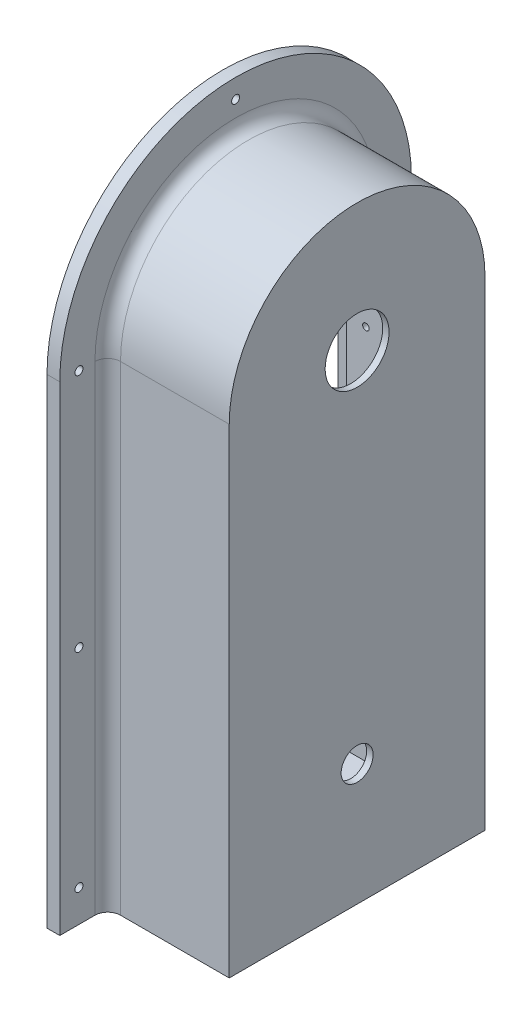
SolidWorks part; units mm, degrees
ref_plane "정면" through (0, 0, 0) normal (0, 0, 1) x (1, 0, 0)
ref_plane "윗면" through (0, 0, 0) normal (0, 1, 0) x (1, 0, 0)
ref_plane "우측면" through (0, 0, 0) normal (1, 0, 0) x (0, 0, -1)
ref_plane "평면1" through (0, 35.25, 0) normal (0, -1, 0) x (1, 0, 0)
sketch "스케치1" plane through (0, 35.25, 0) normal (0, -1, 0) x (1, 0, 0)
  line L0 (-19, -14.25) -> (-23, -14.25)
  line L1 (-23, -14.25) -> (-23, -69.25)
  line L2 (-23, -69.25) -> (-19, -69.25)
  line L3 (-19, -69.25) -> (-19, -14.25)
  line L4 (-18.9999, -14.25) -> (-23.0001, -14.25) construction
revolve "회전1" add sketch "스케치1" angle 180 about L4
sketch "스케치2" plane through (0, 35.25, 0) normal (0, -1, 0) x (1, 0, 0)
  line L0 (-19, -69.25) -> (-23, -69.25)
  line L1 (-23, -69.25) -> (-23, 40.75)
  line L2 (-23, 40.75) -> (-19, 40.75)
  line L3 (-19, 40.75) -> (-19, -69.25)
extrude "보스-돌출1" add sketch "스케치2" along normal blind 150
sketch "스케치3" plane through (-19, 0, 0) normal (1, 0, 0) x (0, 0, -1)
  line L0 (-25.75, -114.75) -> (-25.75, 35.25)
  line L1 (54.25, 35.25) -> (54.25, -114.75)
  line L2 (54.25, -114.75) -> (-25.75, -114.75)
  arc A0 (-25.75, 35.25) -> (54.25, 35.25) centre (14.25, 35.25) cw
extrude "보스-돌출2" add sketch "스케치3" along normal blind 38
sketch "스케치4" plane through (-23, 0, 0) normal (-1, 0, 0) x (0, 0, 1)
  line L0 (-50.25, -110.75) -> (21.75, -110.75)
  line L1 (21.75, -110.75) -> (21.75, 35.25)
  line L2 (-50.25, 35.25) -> (-50.25, -110.75)
  arc A0 (21.75, 35.25) -> (-50.25, 35.25) centre (-14.25, 35.25) ccw
extrude "컷-돌출1" cut sketch "스케치4" against normal blind 40
sketch "스케치5" plane through (17, 0, 0) normal (-1, 0, 0) x (0, 0, 1)
  line L0 (4, 50.5) -> (4, -4)
  line L1 (4, -4) -> (-32.5, -4)
  line L2 (-32.5, -4) -> (-32.5, 50.5)
  line L3 (-32.5, 50.5) -> (4, 50.5)
extrude "보스-돌출3" add sketch "스케치5" along normal blind 17
sketch "스케치6" plane through (0, 0, 0) normal (-1, 0, 0) x (0, 0, 1)
  line L0 (-30, -1.5) -> (1.5, -1.5)
  line L1 (1.5, -1.5) -> (1.5, 48)
  line L2 (1.5, 48) -> (-30, 48)
  line L3 (-30, 48) -> (-30, -1.5)
extrude "컷-돌출2" cut sketch "스케치6" against normal blind 17
hole_wizard "Ø20.0 (20) 지름 구멍1" positions "스케치8" profile "스케치7" hole size "Ø20.0" standard "Ansi Metric"
sketch "스케치8" plane through (17, 0, 0) normal (-1, 0, 0) x (0, 0, 1)
  point P0 (-14.25, 35.25)
sketch "스케치7" plane through (17, 35.25, -14.25) normal (0, 1, 0) x (0, 0, 1)
  line L0 (0, 0) -> (0, 2)
  line L1 (0, 2) -> (10, 2)
  line L2 (10, 2) -> (10, 0)
  line L5 (10, 0) -> (0, 0)
  line L11 (0, -6.35) -> (0, 107.95) construction
  dimension "관통 구멍 지름" = 20
  dimension "관통 구멍 깊이" = 2
hole_wizard "Ø10.0 (10) 지름 구멍1" positions "스케치10" profile "스케치9" hole size "Ø10.0" standard "Ansi Metric"
sketch "스케치10" plane through (17, 0, 0) normal (-1, 0, 0) x (0, 0, 1)
  point P0 (-14.25, -76.75)
sketch "스케치9" plane through (17, -76.75, -14.25) normal (0, 1, 0) x (0, 0, 1)
  line L0 (0, 0) -> (0, 2)
  line L1 (0, 2) -> (5, 2)
  line L2 (5, 2) -> (5, 0)
  line L5 (5, 0) -> (0, 0)
  line L11 (0, -6.35) -> (0, 107.95) construction
  dimension "관통 구멍 지름" = 10
  dimension "관통 구멍 깊이" = 2
hole_wizard "Ø2.5 (2.5) 지름 구멍1" positions "스케치12" profile "스케치11" hole size "Ø2.5" standard "Ansi Metric"
sketch "스케치12" plane through (-19, 0, 0) normal (1, 0, 0) x (0, 0, -1)
  point P0 (-34.75, -104.75)
  point P1 (63.25, -104.75)
  point P2 (63.25, -39.75)
  point P3 (63.25, 35.25)
  point P4 (-34.75, 35.25)
  point P5 (-34.75, -39.75)
  point P6 (14.25, 84.25)
sketch "스케치11" plane through (-19, -104.75, 34.75) normal (0, 1, 0) x (0, 0, -1)
  line L0 (0, 0) -> (0, 4)
  line L1 (0, 4) -> (1.25, 4)
  line L2 (1.25, 4) -> (1.25, 0)
  line L5 (1.25, 0) -> (0, 0)
  line L11 (0, -6.35) -> (0, 107.95) construction
  dimension "관통 구멍 지름" = 2.5
  dimension "관통 구멍 깊이" = 4
hole_wizard "Ø2.05 (2.05) 지름 구멍1" positions "스케치14" profile "스케치13" hole size "Ø2.05" standard "Ansi Metric"
sketch "스케치14" plane through (0, -1.5, 0) normal (0, 1, 0) x (1, 0, 0)
  point P0 (6, 6.25)
  point P1 (6, 22.25)
sketch "스케치13" plane through (6, -1.5, -6.25) normal (1, 0, 0) x (0, 0, 1)
  line L0 (0, 0) -> (0, 2.5)
  line L1 (0, 2.5) -> (1.025, 2.5)
  line L2 (1.025, 2.5) -> (1.025, 0)
  line L5 (1.025, 0) -> (0, 0)
  line L11 (0, -6.35) -> (0, 107.95) construction
  dimension "관통 구멍 지름" = 2.05
  dimension "관통 구멍 깊이" = 2.5
hole_wizard "Ø2.05 (2.05) 지름 구멍2" positions "스케치16" profile "스케치15" hole size "Ø2.05" standard "Ansi Metric"
sketch "스케치16" plane through (0, 0, 1.5) normal (0, 0, -1) x (-1, 0, 0)
  point P0 (-6, 27.25)
  point P1 (-6, 3.25)
sketch "스케치15" plane through (6, 27.25, 1.5) normal (1, 0, 0) x (0, 1, 0)
  line L0 (0, 0) -> (0, 2.5)
  line L1 (0, 2.5) -> (1.025, 2.5)
  line L2 (1.025, 2.5) -> (1.025, 0)
  line L5 (1.025, 0) -> (0, 0)
  line L11 (0, -6.35) -> (0, 107.95) construction
  dimension "관통 구멍 지름" = 2.05
  dimension "관통 구멍 깊이" = 2.5
hole_wizard "Ø2.05 (2.05) 지름 구멍3" positions "스케치18" profile "스케치17" hole size "Ø2.05" standard "Ansi Metric"
sketch "스케치18" plane through (0, 48, 0) normal (0, -1, 0) x (-1, 0, 0)
  point P0 (-6, 6.25)
  point P1 (-6, 22.25)
sketch "스케치17" plane through (6, 48, -6.25) normal (1, 0, 0) x (0, 0, -1)
  line L0 (0, 0) -> (0, 2.5)
  line L1 (0, 2.5) -> (1.025, 2.5)
  line L2 (1.025, 2.5) -> (1.025, 0)
  line L5 (1.025, 0) -> (0, 0)
  line L11 (0, -6.35) -> (0, 107.95) construction
  dimension "관통 구멍 지름" = 2.05
  dimension "관통 구멍 깊이" = 2.5
hole_wizard "Ø2.05 (2.05) 지름 구멍4" positions "스케치20" profile "스케치19" hole size "Ø2.05" standard "Ansi Metric"
sketch "스케치20" plane through (0, 0, -30) normal (0, 0, 1) x (1, 0, 0)
  point P0 (6, 27.25)
  point P1 (6, 3.25)
sketch "스케치19" plane through (6, 27.25, -30) normal (1, 0, 0) x (0, -1, 0)
  line L0 (0, 0) -> (0, 2.5)
  line L1 (0, 2.5) -> (1.025, 2.5)
  line L2 (1.025, 2.5) -> (1.025, 0)
  line L5 (1.025, 0) -> (0, 0)
  line L11 (0, -6.35) -> (0, 107.95) construction
  dimension "관통 구멍 지름" = 2.05
  dimension "관통 구멍 깊이" = 2.5
fillet "필렛1" radius 4 3 edges at (-19, -39.75, 25.75) (-19, -39.75, -54.25) (-19, 75.25, -14.25)
